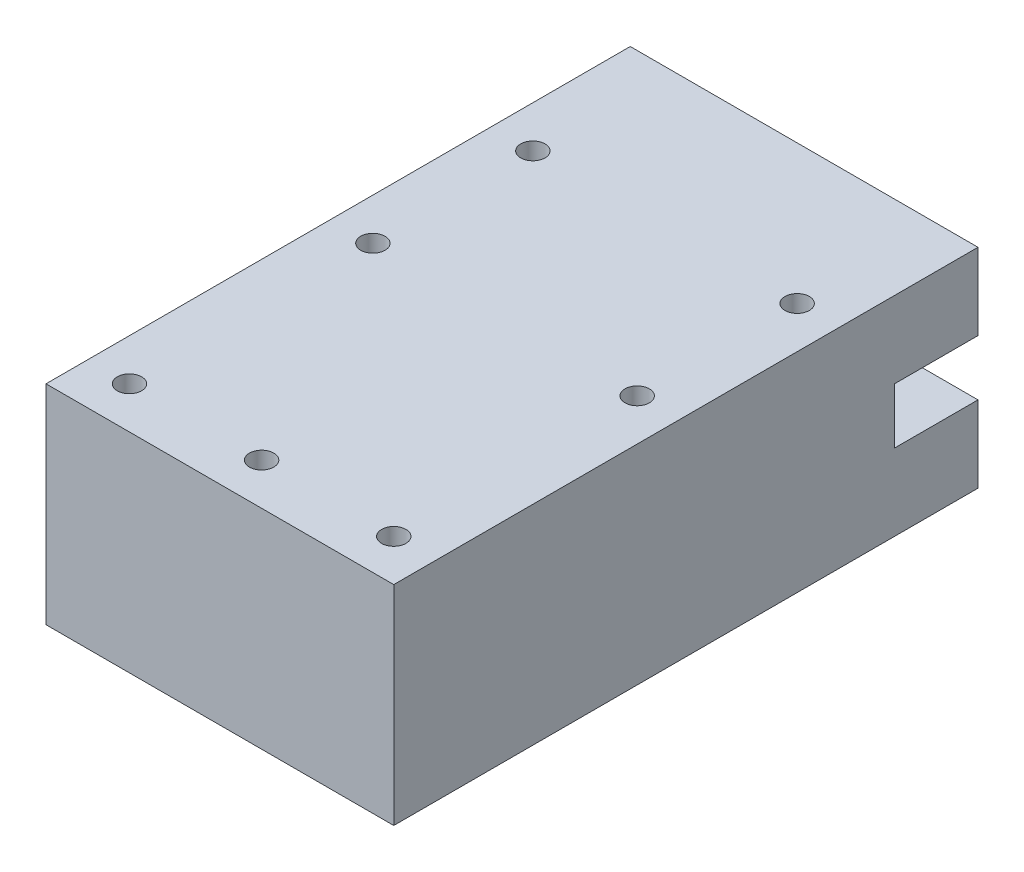
SolidWorks part; units mm, degrees
ref_plane "正面" through (0, 0, 0) normal (0, 0, 1) x (1, 0, 0)
ref_plane "平面" through (0, 0, 0) normal (0, 1, 0) x (1, 0, 0)
ref_plane "右側面" through (0, 0, 0) normal (1, 0, 0) x (0, 0, -1)
sketch "ｽｹｯﾁ1" plane through (0, 0, 0) normal (0, 0, 1) x (1, 0, 0)
  line L1 (-25, 15) -> (25, 15)
  line L2 (-25, 15) -> (-25, -15)
  line L3 (-25, -15) -> (25, -15)
  line L4 (25, 15) -> (25, -15)
  line L5 (-25, 15) -> (25, -15) construction
  line L6 (-25, -15) -> (25, 15) construction
  point P0 (0, 0)
  dimension "D1" = 30
  dimension "D2" = 50
extrude "ﾎﾞｽ - 押し出し1" add sketch "ｽｹｯﾁ1" along normal blind 84
sketch "ｽｹｯﾁ2" plane through (0, 0, 0) normal (0, 0, -1) x (-1, 0, 0)
  line L1 (13, 7) -> (-13, 7)
  line L2 (13, 7) -> (13, -7)
  line L3 (13, -7) -> (-13, -7)
  line L4 (-13, 7) -> (-13, -7)
  line L5 (13, 7) -> (-13, -7) construction
  line L6 (13, -7) -> (-13, 7) construction
  point P0 (0, 0)
  dimension "D1" = 26
  dimension "D2" = 14
extrude "ｶｯﾄ - 押し出し1" cut sketch "ｽｹｯﾁ2" against normal blind 72
ref_plane "平面1" through (0, 0, 0) normal (0, -1, 0) x (-1, 0, 0)
sketch "ｽｹｯﾁ5" plane through (13, 0, 0) normal (-1, 0, 0) x (0, 0, 1)
  line L0 (0, 7) -> (0, -7) construction
  line L1 (0, 4) -> (12, 4)
  line L2 (0, 4) -> (0, -4)
  line L3 (0, -4) -> (12, -4)
  line L4 (12, 4) -> (12, -4)
  line L6 (84, -15) -> (0, -15) construction
  dimension "D1" = 8
  dimension "D2" = 11
  dimension "D3" = 12
extrude "ｶｯﾄ - 押し出し4" cut sketch "ｽｹｯﾁ5" against normal through all
sketch "ｽｹｯﾁ6" plane through (-13, 0, 0) normal (1, 0, 0) x (0, 0, -1)
  line L0 (0, -7) -> (0, 7) construction
  line L1 (0, 4) -> (-12, 4)
  line L2 (0, 4) -> (0, -4)
  line L3 (0, -4) -> (-12, -4)
  line L4 (-12, 4) -> (-12, -4)
  line L5 (-84, -15) -> (0, -15) construction
  dimension "D1" = 12
  dimension "D2" = 8
  dimension "D3" = 11
extrude "ｶｯﾄ - 押し出し5" cut sketch "ｽｹｯﾁ6" against normal through all
sketch "ｽｹｯﾁ7" plane through (0, 15, 0) normal (0, 1, 0) x (1, 0, 0)
  line L0 (25, -84) -> (25, 0) construction
  line L1 (-25, -84) -> (-25, 0) construction
  line L2 (25, -84) -> (-25, -84) construction
  line L3 (25, 0) -> (-25, 0) construction
  circle A0 centre (19, -20) radius 1.75
  circle A1 centre (19, -43) radius 1.75
  circle A2 centre (19, -78) radius 1.75
  circle A3 centre (0, -78) radius 1.75
  circle A4 centre (-19, -78) radius 1.75
  circle A5 centre (-19, -43) radius 1.75
  circle A6 centre (-19, -20) radius 1.75
  dimension "D1" = 3.5
  dimension "D2" = 3.5
  dimension "D3" = 3.5
  dimension "D4" = 3.5
  dimension "D5" = 3.5
  dimension "D6" = 3.5
  dimension "D7" = 3.5
  dimension "D8" = 6
  dimension "D9" = 6
  dimension "D10" = 6
  dimension "D11" = 6
  dimension "D12" = 6
  dimension "D13" = 6
  dimension "D14" = 6
  dimension "D15" = 6
  dimension "D16" = 6
  dimension "D17" = 20
  dimension "D18" = 20
  dimension "D19" = 23
  dimension "D20" = 23
  dimension "D21" = 19
extrude "ｶｯﾄ - 押し出し7" cut sketch "ｽｹｯﾁ7" against normal through all
